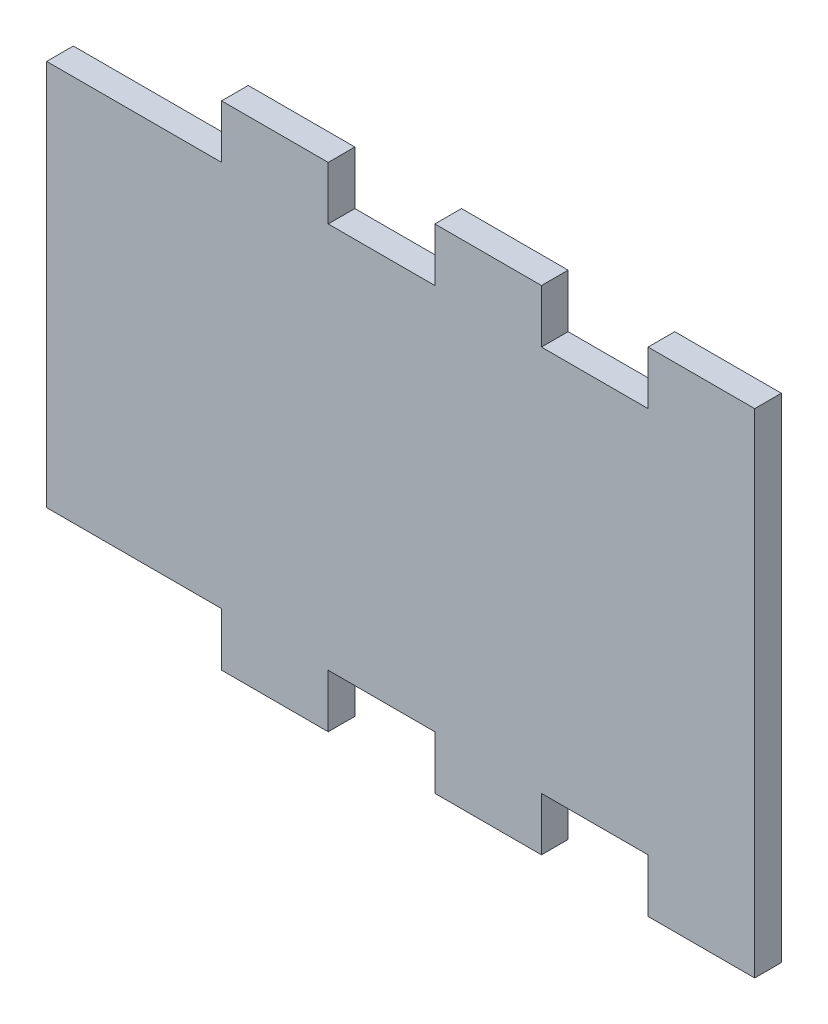
SolidWorks part; units mm, degrees
ref_plane "Front Plane" through (0, 0, 0) normal (0, 0, 1) x (1, 0, 0)
ref_plane "Top Plane" through (0, 0, 0) normal (0, 1, 0) x (1, 0, 0)
ref_plane "Right Plane" through (0, 0, 0) normal (1, 0, 0) x (0, 0, -1)
sketch "Sketch1" plane through (0, 0, 0) normal (0, 0, 1) x (1, 0, 0)
  line L0 (-38.1, 46.035) -> (-38.1, 52.385)
  line L1 (-12.7, 0) -> (-25.4, 0)
  line L2 (0, 0) -> (0, 46.035)
  line L3 (-12.7, 46.035) -> (-25.4, 46.035)
  line L4 (-84.3382, 0) -> (-84.3382, 46.035)
  line L5 (-25.4, 52.385) -> (-38.1, 52.385)
  line L6 (0, 46.035) -> (0, 52.385)
  line L7 (0, 52.385) -> (-12.7, 52.385)
  line L8 (-12.7, 46.035) -> (-12.7, 52.385)
  line L9 (-25.4, 46.035) -> (-25.4, 52.385)
  line L10 (-63.5, 46.035) -> (-63.5, 52.385)
  line L11 (-50.8, 52.385) -> (-63.5, 52.385)
  line L12 (-50.8, 46.035) -> (-50.8, 52.385)
  line L13 (-63.5, 46.035) -> (-76.2, 46.035)
  line L17 (-38.1, 46.035) -> (-50.8, 46.035)
  line L18 (-88.9, 46.035) -> (-88.9, 52.385) [skipped]
  line L19 (-84.3382, 23.0175) -> (0, 23.0175) construction
  line L23 (-63.5, 0) -> (-63.5, -6.35)
  line L24 (-50.8, -6.35) -> (-63.5, -6.35)
  line L25 (-50.8, 0) -> (-50.8, -6.35)
  line L26 (-38.1, 0) -> (-38.1, -6.35)
  line L27 (-25.4, -6.35) -> (-38.1, -6.35)
  line L28 (-25.4, 0) -> (-25.4, -6.35)
  line L29 (-12.7, 0) -> (-12.7, -6.35)
  line L30 (0, -6.35) -> (-12.7, -6.35)
  line L31 (0, 0) -> (0, -6.35)
  line L32 (-63.5, 0) -> (-76.2, 0)
  line L33 (-38.1, 0) -> (-50.8, 0)
  line L34 (-76.2, 46.035) -> (-84.3382, 46.035)
  line L35 (-76.2, 0) -> (-84.3382, 0)
  line L37 (-76.2, 52.385) -> (-84.3382, 52.385) [skipped]
  line L38 (-76.2, 46.035) -> (-76.2, 52.385) [skipped]
  dimension "D1" = 46.035
  dimension "D2" = 84.3382
  dimension "D3" = 6.35
  dimension "D4" = 12.7
  dimension "D5" = 4
extrude "Boss-Extrude1" add sketch "Sketch1" along normal blind 3.175
